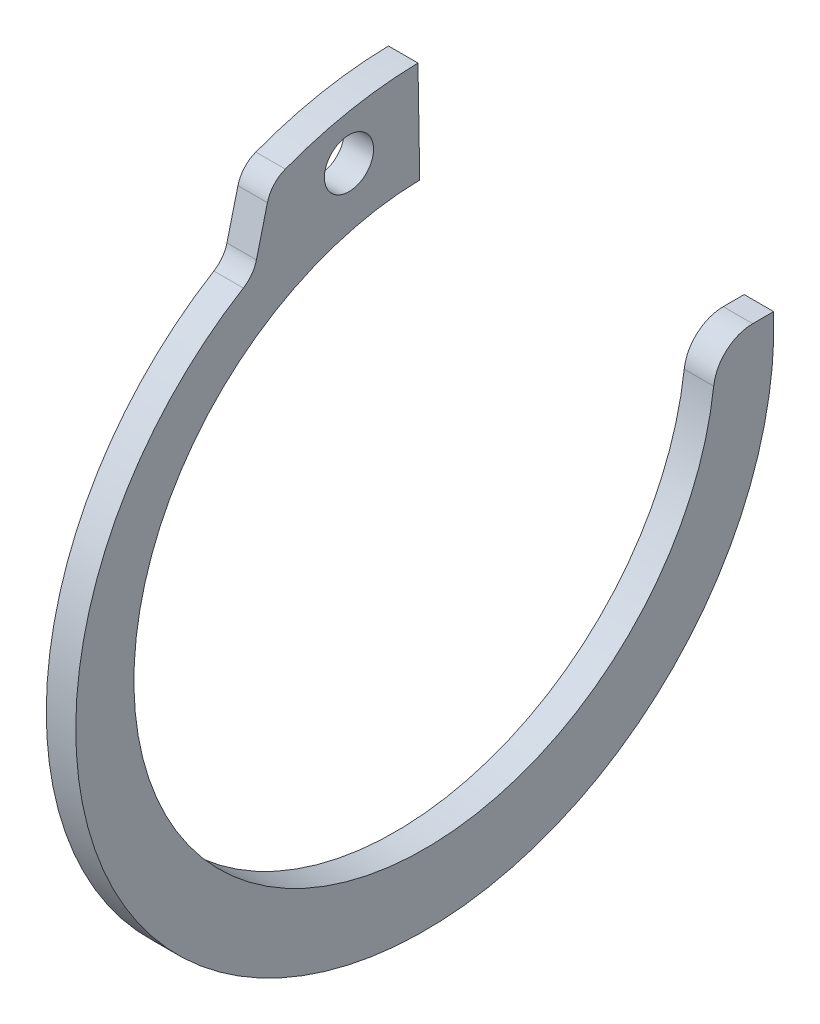
SolidWorks part; units mm, degrees
ref_plane "Front" through (0, 0, 0) normal (0, 0, 1) x (1, 0, 0)
ref_plane "Top" through (0, 0, 0) normal (0, 1, 0) x (1, 0, 0)
ref_plane "Right" through (0, 0, 0) normal (1, 0, 0) x (0, 0, -1)
sketch "Sketch1" plane through (0, 0, 0) normal (1, 0, 0) x (0, 0, -1)
  line L0 (0, 0) -> (0, 14.8) construction
  line L1 (-0.2583, 14.7977) -> (-0.349, 19.997)
  line L2 (-0.349, 19.997) -> (-7.4593, 19.8728) construction
  line L3 (-7.4593, 19.8728) -> (-8.7173, 14.8273) construction
  line L4 (0.349, 19.997) -> (0.2583, 14.7977)
  line L5 (0.349, 19.997) -> (7.4593, 19.8728) construction
  line L6 (7.4593, 19.8728) -> (8.7173, 14.8273) construction
  line L7 (-8.7173, 14.8273) -> (-7.5009, 12.7584) construction
  line L8 (8.7173, 14.8273) -> (7.5009, 12.7584) construction
  line L9 (0, -14.8) -> (0, -18.4) construction
  line L10 (-7.4593, 19.8728) -> (-0.2583, 14.7977) construction
  line L12 (0, 14.8) -> (0, 20) construction
  line L13 (7.8251, 18.4056) -> (8.7173, 14.8273)
  line L14 (-7.8251, 18.4056) -> (-8.7173, 14.8273)
  circle A0 centre (0, 0) radius 14.8 construction
  arc A1 (-0.2583, 14.7977) -> (0.2583, 14.7977) centre (0, 0) ccw
  circle A2 centre (0, -0.6428) radius 17.7572 construction
  circle A4 centre (-3.8588, 17.3353) radius 1.25
  circle A5 centre (3.8588, 17.3353) radius 1.25
  arc A6 (-8.7173, 14.8273) -> (8.7173, 14.8273) centre (0, -0.6428) ccw
  arc A7 (0.349, 19.997) -> (7.8251, 18.4056) centre (0, 0) cw
  arc A8 (-0.349, 19.997) -> (-7.8251, 18.4056) centre (0, 0) ccw
  dimension "D1" = 75
  dimension "A" = 29.6
  dimension "Hole" = 2.5
  dimension "Smin" = 2.4
  dimension "Smax" = 3.6
  dimension "H" = 5.2
  dimension "Angle" = 1
extrude "Extrude1" add sketch "Sketch1" along normal mid plane 1.5
fillet "Fillet1" radius 1.48 4 edges at (0, 14.8273, 8.7173) (0, 18.4056, 7.8251) (0, 18.4056, -7.8251) (0, 14.8273, -8.7173)
sketch "Sketch2" plane through (0, 0, 0) normal (0, 0, 1) x (1, 0, 0)
  line L0 (-4, 0) -> (12, 0)
  line L1 (12, 0) -> (12, -16)
  line L2 (-4, 0) -> (-4, -15.15)
  line L3 (12, -16) -> (0.8, -16)
  line L4 (0.8, -16) -> (0.8, -15.15)
  line L5 (0.8, -15.15) -> (-0.8, -15.15)
  line L6 (-0.8, -15.15) -> (-0.8, -16)
  line L7 (-0.8, -16) -> (-4, -16) construction
  line L8 (-4, -16) -> (-4, 0) construction
  line L9 (0, -15.15) -> (0, 0) construction
  line L10 (12, 0) -> (14.0551, 0) construction
  line L11 (-4, -15.15) -> (-3.15, -16)
  line L12 (-3.15, -16) -> (-0.8, -16)
  dimension "D1" = 45
  dimension "Dg" = 30.3
  dimension "Ds" = 32
  dimension "D2" = 16
  dimension "W" = 1.6
  dimension "D3" = 4
revolve "Revolve1" [suppressed] add sketch "Sketch2" angle 360 about L10
sketch "Sketch3" plane through (0.75, 0, 0) normal (1, 0, 0) x (0, 0, -1)
  line L0 (0, 0) -> (0, 37.6594)
  line L1 (0, 0) -> (33.9449, 0)
  line L2 (0, 37.6594) -> (33.9449, 0)
  dimension "D1" = 90
extrude "Cut-Extrude1" cut sketch "Sketch3" against normal through all
fillet "Fillet2" radius 2 1 edges at (0, 0, -14.8)
equation "\"D2@Sketch2\" = \"W@Sketch2\"*10"
equation "\"D3@Sketch2\" = \"D2@Sketch2\"/4"
equation "\"Smin@Sketch1\" = \"Smax@Sketch1\"/1.5"
